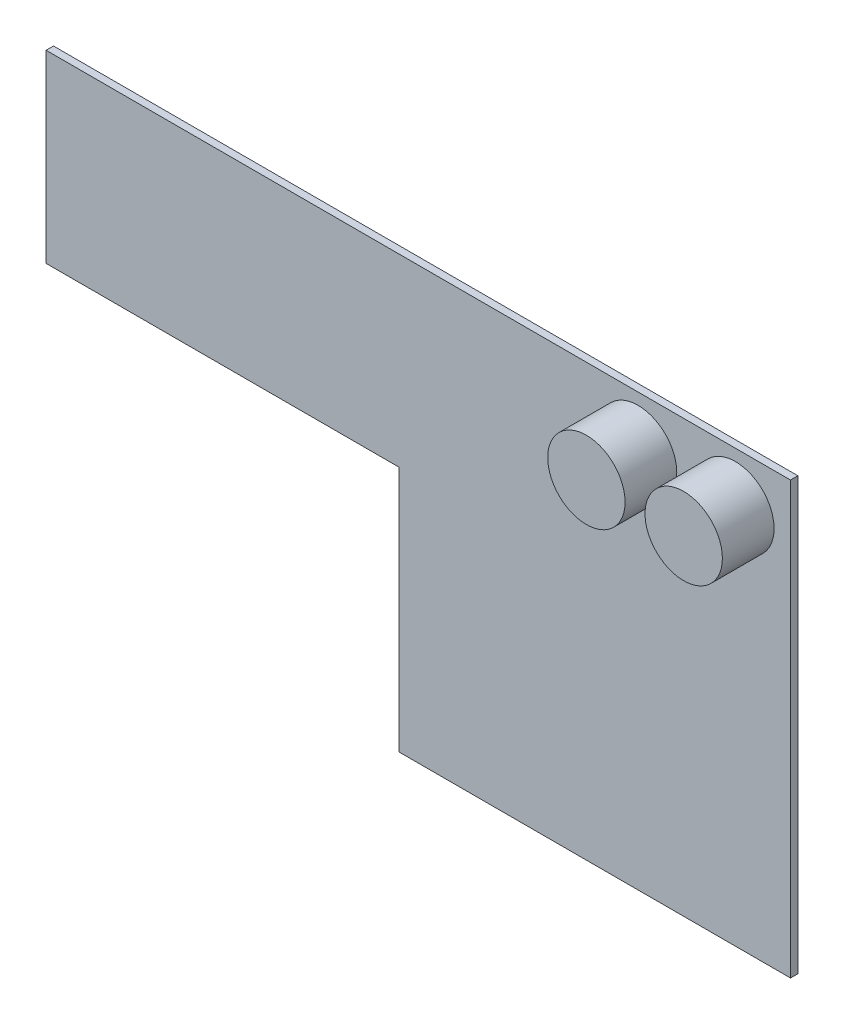
SolidWorks part; units mm, degrees
ref_plane "Front Plane" through (0, 0, 0) normal (0, 0, 1) x (1, 0, 0)
ref_plane "Top Plane" through (0, 0, 0) normal (0, 1, 0) x (1, 0, 0)
ref_plane "Right Plane" through (0, 0, 0) normal (1, 0, 0) x (0, 0, -1)
sketch "Sketch1" plane through (0, 0, 0) normal (0, 0, 1) x (1, 0, 0)
  line L0 (0, 0) -> (265, 0)
  line L1 (265, 0) -> (265, 292)
  line L2 (265, 292) -> (-239, 292)
  line L3 (-239, 292) -> (-239, 167)
  line L4 (-239, 167) -> (0, 167)
  line L5 (0, 167) -> (0, 0)
  dimension "D1" = 265
  dimension "D2" = 292
  dimension "D3" = 504
  dimension "D4" = 125
extrude "Boss-Extrude1" add sketch "Sketch1" along normal blind 5
sketch "Sketch2" plane through (0, 0, 5) normal (0, 0, 1) x (1, 0, 0)
  circle A0 centre (227.6864, 257.9935) radius 26.1938
  circle A1 centre (161.8079, 257.9935) radius 26.1938
  dimension "D1" = 52.3875
extrude "Boss-Extrude2" add sketch "Sketch2" along normal blind 35
